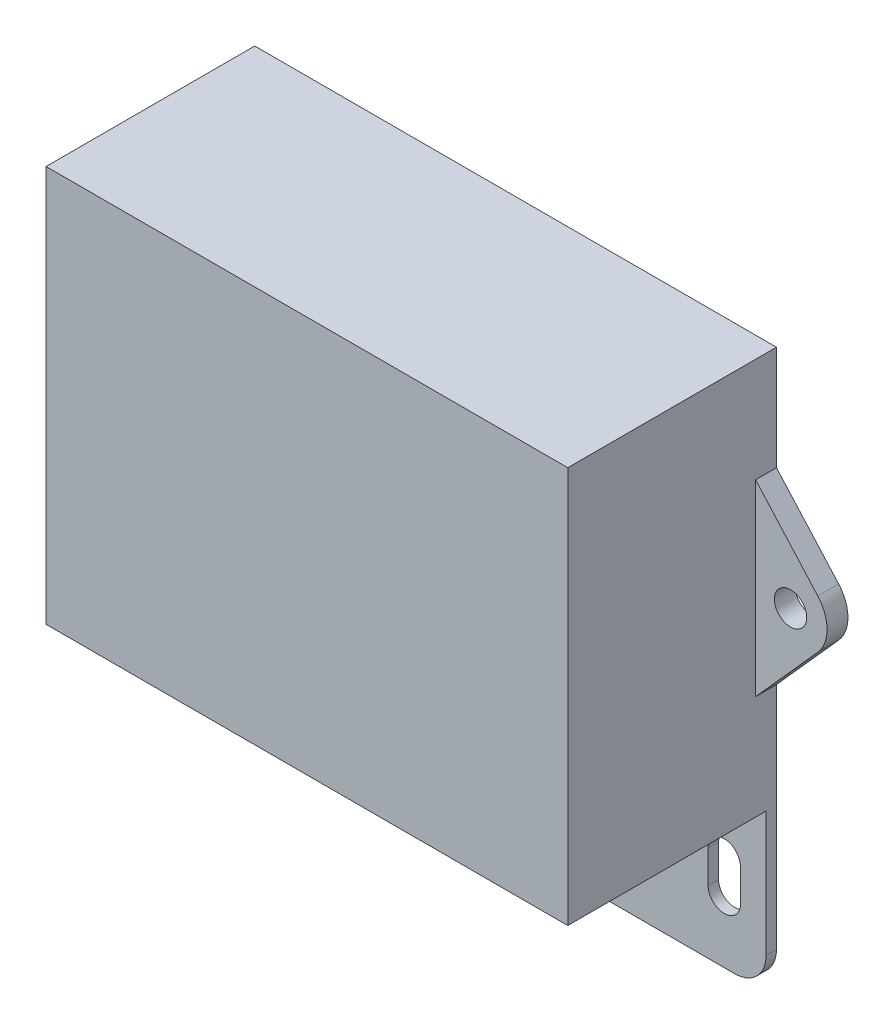
SolidWorks part; units mm, degrees
ref_plane "Front Plane" through (0, 0, 0) normal (0, 0, 1) x (1, 0, 0)
ref_plane "Top Plane" through (0, 0, 0) normal (0, 1, 0) x (1, 0, 0)
ref_plane "Right Plane" through (0, 0, 0) normal (1, 0, 0) x (0, 0, -1)
sketch "Sketch1" plane through (0, 0, 0) normal (0, 0, 1) x (1, 0, 0)
  line L1 (-25, 19) -> (25, 19)
  line L2 (-25, 19) -> (-25, -19)
  line L3 (-25, -19) -> (25, -19)
  line L4 (25, 19) -> (25, -19)
  line L5 (-25, 19) -> (25, -19) construction
  line L6 (-25, -19) -> (25, 19) construction
  point P0 (0, 0)
  dimension "D1" = 50
  dimension "D2" = 38
extrude "MAIN BODY" add sketch "Sketch1" along normal mid plane 20
sketch "Sketch2" plane through (0, 0, -10) normal (0, 0, -1) x (-1, 0, 0)
  line L0 (28.35, 0) -> (31.85, 0) construction
  line L1 (30.9595, -2.3324) -> (25, -9)
  line L2 (30.9595, 2.3324) -> (25, 9)
  line L3 (-25, 19) -> (25, 19) construction
  line L4 (25, 19) -> (25, -19) construction
  line L5 (25, -9) -> (25, 9)
  arc A0 (30.9595, -2.3324) -> (30.9595, 2.3324) centre (28.35, 0) ccw
  dimension "D3" = 3.5
  dimension "D1" = 19
  dimension "D2" = 6.85
  dimension "D4" = 18
extrude "SIDE MOUNTING BODY" add sketch "Sketch2" against normal blind 2
mirror "Mirror1" about plane through (0, 0, 0) normal (1, 0, 0) of "SIDE MOUNTING BODY"
hole_wizard "Ø3.1 (3.1) Diameter Hole1" positions "Sketch4" profile "Sketch3" hole size "Ø3.1" standard "ANSI Metric" end condition through all
sketch "Sketch4" plane through (0, 0, -8) normal (0, 0, 1) x (1, 0, 0)
  line L0 (-28.35, 0) -> (28.35, 0) construction
  arc A0 (-30.9595, 2.3324) -> (-30.9595, -2.3324) centre (-28.35, 0) ccw construction
  arc A1 (30.9595, -2.3324) -> (30.9595, 2.3324) centre (28.35, 0) ccw construction
  point P0 (-28.35, 0)
  point P2 (28.35, 0)
sketch "Sketch3" plane through (-28.35, 0, -8) normal (1, 0, 0) x (0, -1, 0)
  line L0 (0, 0) -> (0, 2)
  line L1 (0, 2) -> (1.55, 2)
  line L2 (1.55, 2) -> (1.55, 0)
  line L5 (1.55, 0) -> (0, 0)
  line L11 (0, -6.35) -> (0, 107.95) construction
  dimension "Thru Hole Dia." = 3.1
  dimension "Thru Hole Depth" = 2
sketch "Sketch5" plane through (0, -19, 0) normal (0, -1, 0) x (-1, 0, 0)
  line L0 (25, -10) -> (-25, -10) construction
  line L1 (24, -9) -> (-24, -9)
  line L2 (24, -9) -> (24, 9)
  line L3 (24, 9) -> (-24, 9)
  line L4 (-24, -9) -> (-24, 9)
  line L5 (24, -9) -> (-24, 9) construction
  line L6 (24, 9) -> (-24, -9) construction
  line L7 (25, -10) -> (25, 10) construction
  point P0 (0, 0)
  dimension "D1" = 1
  dimension "D2" = 1
extrude "BOTTOM CUT" cut sketch "Sketch5" against normal blind 2.6
sketch "Sketch6" plane through (0, -19, 0) normal (0, -1, 0) x (-1, 0, 0)
  line L0 (-25, -10) -> (-25, 10) construction
  line L1 (25, 10) -> (-25, 10)
  line L2 (25, 10) -> (25, 9)
  line L3 (25, 9) -> (-25, 9)
  line L4 (-25, 10) -> (-25, 9)
  line L5 (24, 9) -> (-24, 9) construction
extrude "BOTTOM MOUNTING TAB" add sketch "Sketch6" along normal blind 15
sketch "Sketch7" plane through (0, 0, -9) normal (0, 0, 1) x (1, 0, 0)
  line L0 (-21, -24.85) -> (-21, -27.95) construction
  line L1 (-19.45, -24.85) -> (-19.45, -27.95)
  line L2 (-22.55, -24.85) -> (-22.55, -27.95)
  line L3 (25, -34) -> (-25, -34) construction
  line L4 (-25, -34) -> (-25, -19) construction
  arc A0 (-19.45, -24.85) -> (-22.55, -24.85) centre (-21, -24.85) ccw
  arc A1 (-22.55, -27.95) -> (-19.45, -27.95) centre (-21, -27.95) ccw
  point P2 (-21, -26.4)
  dimension "D1" = 3.1
  dimension "D2" = 3.1
  dimension "D3" = 6.05
  dimension "D4" = 4
extrude "SLOT" cut sketch "Sketch7" against normal through all
mirror "Mirror2" about plane through (0, 0, 0) normal (1, 0, 0) of "SLOT"
fillet "Fillet1" radius 1.5 8 edges at (0, -16.4, -9) (-24, -16.4, 0) (0, -16.4, 9) (24, -16.4, 0) (24, -17.7, -9) (-24, -17.7, -9) (-24, -17.7, 9) (24, -17.7, 9)
fillet "Fillet2" radius 3 2 edges at (25, -34, -9.5) (-25, -34, -9.5)
